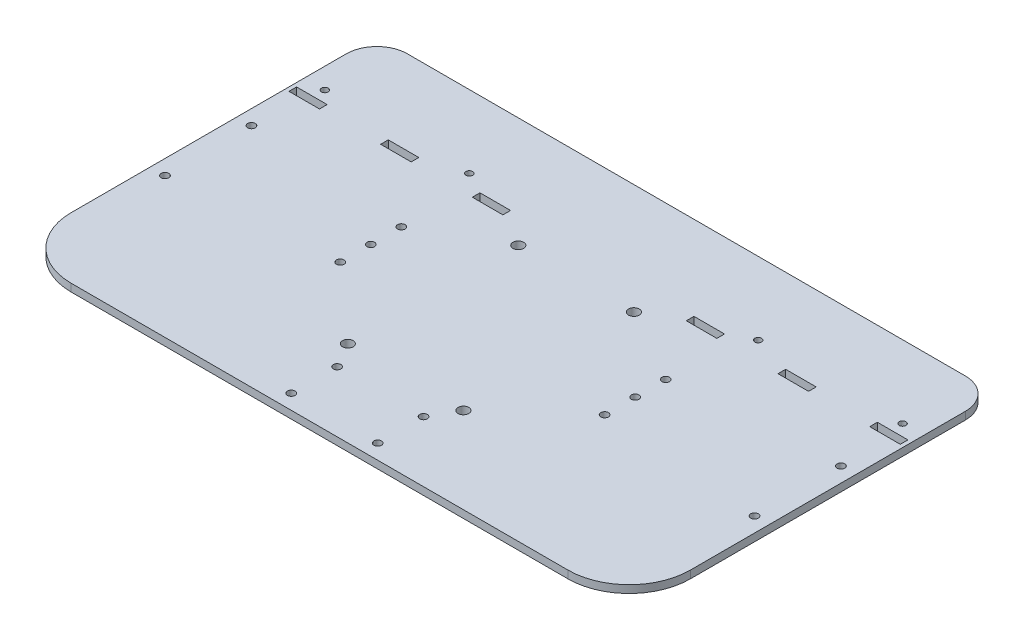
SolidWorks part; units mm, degrees
ref_plane "Front Plane" through (0, 0, 0) normal (0, 0, 1) x (1, 0, 0)
ref_plane "Top Plane" through (0, 0, 0) normal (0, 1, 0) x (1, 0, 0)
ref_plane "Right Plane" through (0, 0, 0) normal (1, 0, 0) x (0, 0, -1)
sketch "Sketch1" plane through (0, 0, 0) normal (0, 1, 0) x (1, 0, 0)
  line L0 (257.2387, -695.2) -> (257.2387, 49304.8) construction
  line L1 (50.8, 0) -> (463.6775, 0)
  line L2 (0, 50.8) -> (0, 279.4)
  line L3 (25.4, 304.8) -> (489.0775, 304.8)
  line L4 (514.4775, 50.8) -> (514.4775, 279.4)
  line L5 (511.1755, 228.5746) -> (485.7755, 228.5746)
  line L6 (511.1755, 228.5746) -> (511.1755, 234.9246)
  line L7 (511.1755, 234.9246) -> (485.7755, 234.9246)
  line L8 (485.7755, 228.5746) -> (485.7755, 234.9246)
  line L9 (434.9755, 228.5746) -> (409.5755, 228.5746)
  line L10 (434.9755, 228.5746) -> (434.9755, 234.9246)
  line L11 (434.9755, 234.9246) -> (409.5755, 234.9246)
  line L12 (409.5755, 228.5746) -> (409.5755, 234.9246)
  line L13 (358.7755, 228.5746) -> (333.3755, 228.5746)
  line L14 (358.7755, 228.5746) -> (358.7755, 234.9246)
  line L15 (358.7755, 234.9246) -> (333.3755, 234.9246)
  line L16 (333.3755, 228.5746) -> (333.3755, 234.9246)
  line L17 (180.9755, 228.5746) -> (155.5755, 228.5746)
  line L18 (180.9755, 228.5746) -> (180.9755, 234.9246)
  line L19 (180.9755, 234.9246) -> (155.5755, 234.9246)
  line L20 (155.5755, 228.5746) -> (155.5755, 234.9246)
  line L21 (104.7755, 228.5746) -> (79.3755, 228.5746)
  line L22 (104.7755, 228.5746) -> (104.7755, 234.9246)
  line L23 (104.7755, 234.9246) -> (79.3755, 234.9246)
  line L24 (79.3755, 228.5746) -> (79.3755, 234.9246)
  line L25 (28.5755, 228.5746) -> (3.1755, 228.5746)
  line L26 (28.5755, 228.5746) -> (28.5755, 234.9246)
  line L27 (28.5755, 234.9246) -> (3.1755, 234.9246)
  line L28 (3.1755, 228.5746) -> (3.1755, 234.9246)
  line L29 (147.3962, 215.8746) -> (147.3962, 88.8746) construction
  line L30 (156.0962, 215.8746) -> (138.6962, 215.8746) construction
  line L31 (156.0962, 88.8746) -> (138.6962, 88.8746) construction
  circle A0 centre (305.327, 213.0551) radius 4.445
  circle A1 centre (305.327, 71.4251) radius 4.445
  circle A2 centre (502.1739, 116.4574) radius 3.175
  circle A3 centre (502.1739, 188.2918) radius 3.175
  circle A4 centre (12.3031, 116.4574) radius 3.175
  circle A5 centre (12.3031, 188.2918) radius 3.175
  circle A6 centre (209.277, 71.4251) radius 4.445
  circle A7 centre (209.277, 213.0551) radius 4.445
  circle A8 centre (221.3848, 50.4031) radius 3.175
  circle A9 centre (221.3848, 12.3031) radius 3.175
  circle A10 centre (293.2192, 50.4031) radius 3.175
  circle A11 centre (293.2192, 12.3031) radius 3.175
  circle A12 centre (147.3962, 177.7746) radius 3.175
  circle A13 centre (147.3962, 126.9746) radius 3.175
  circle A14 centre (147.3962, 152.3746) radius 3.175
  circle A15 centre (367.0813, 152.3746) radius 3.175
  circle A16 centre (367.0813, 126.9746) radius 3.175
  circle A17 centre (367.0813, 177.7746) radius 3.175
  circle A18 centre (497.1755, 244.4496) radius 2.794
  circle A19 centre (377.1755, 244.4496) radius 2.794
  circle A20 centre (137.1755, 244.4496) radius 2.794
  circle A21 centre (17.1755, 244.4496) radius 2.794
  arc A22 (463.6775, 0) -> (514.4775, 50.8) centre (463.6775, 50.8) ccw
  arc A23 (50.8, 0) -> (0, 50.8) centre (50.8, 50.8) cw
  arc A24 (0, 279.4) -> (25.4, 304.8) centre (25.4, 279.4) cw
  arc A25 (489.0775, 304.8) -> (514.4775, 279.4) centre (489.0775, 279.4) cw
  point P92 (257.2387, 304.8)
  point P119 (0, 0)
  dimension "D1" = 50.8
  dimension "D2" = 50.8
  dimension "D3" = 25.4
extrude "Boss-Extrude1" add sketch "Sketch1" along normal blind 6.35
